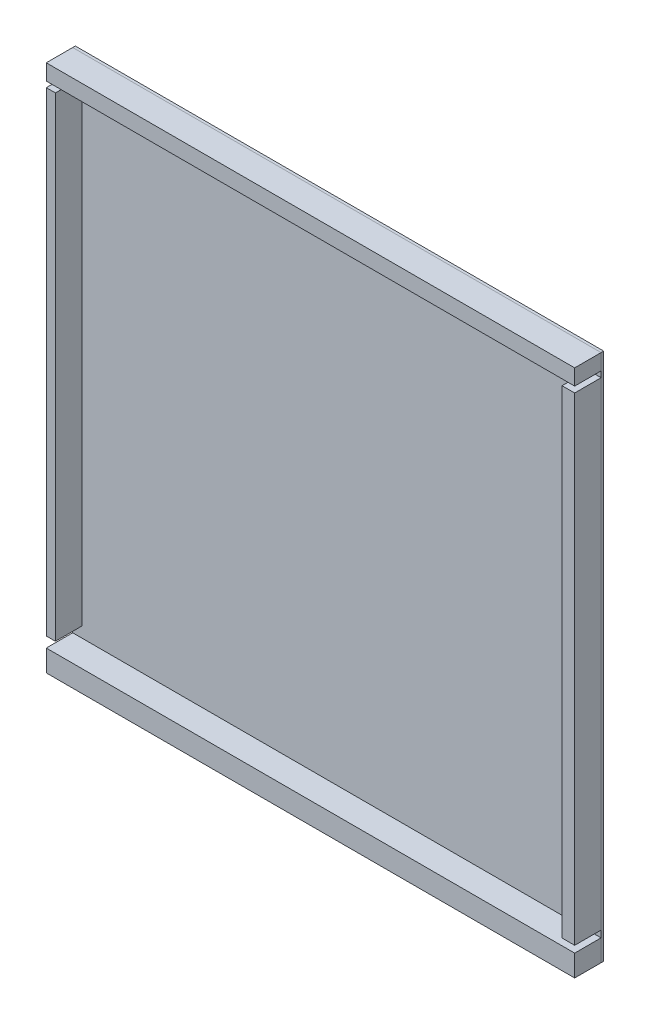
SolidWorks part; units mm, degrees
other "COLL.BOX-Boss-Extrude2"
other "COLL.BOX-Boss-Extrude3"
other "COLL.BOX-Boss-Extrude4"
other "COLL.BOX-Boss-Extrude5"
other "COLL.BOX-Boss-Extrude6"
ref_plane "Front Plane" through (0, 0, 0) normal (0, 0, 1) x (1, 0, 0)
ref_plane "Top Plane" through (0, 0, 0) normal (0, 1, 0) x (1, 0, 0)
ref_plane "Right Plane" through (0, 0, 0) normal (1, 0, 0) x (0, 0, -1)
sketch "Sketch1" plane through (0, 0, 0) normal (0, 0, 1) x (1, 0, 0)
  line L1 (-250, 1750) -> (1750, 1750)
  line L2 (-250, 1750) -> (-250, -250)
  line L3 (-250, -250) -> (1750, -250)
  line L4 (1750, 1750) -> (1750, -250)
  dimension "D1" = 2000
  dimension "D2" = 2000
  dimension "D3" = 250
  dimension "D4" = 250
extrude "Boss-Extrude1" add sketch "Sketch1" along normal blind 10
sketch "Sketch2" plane through (0, 0, 10) normal (0, 0, 1) x (1, 0, 0)
  line L1 (-250, 1750) -> (1750, 1750)
  line L2 (-250, 1750) -> (-250, -250)
  line L3 (-250, -250) -> (1750, -250)
  line L4 (1750, 1750) -> (1750, -250)
extrude "Boss-Extrude2" add sketch "Sketch2" against normal up to next (10 mm away) separate body
sketch "Sketch3" plane through (0, 0, 10) normal (0, 0, 1) x (1, 0, 0)
  line L0 (1750, -250) -> (1750, 1750) construction
  line L1 (-250, 1750) -> (1750, 1750)
  line L2 (-250, 1750) -> (-250, 1690.1338)
  line L3 (-250, 1690.1338) -> (1750, 1690.1338)
  line L4 (1750, 1750) -> (1750, 1690.1338)
extrude "Boss-Extrude3" add sketch "Sketch3" along normal blind 100 separate body
sketch "Sketch4" plane through (0, 0, 10) normal (0, 0, 1) x (1, 0, 0)
  line L0 (-250, 1750) -> (-250, -250) construction
  line L1 (1750, -250) -> (-250, -250)
  line L2 (1750, -250) -> (1750, -168.4149)
  line L3 (1750, -168.4149) -> (-250, -168.4149)
  line L4 (-250, -250) -> (-250, -168.4149)
extrude "Boss-Extrude4" add sketch "Sketch4" along normal blind 100 separate body
sketch "Sketch5" plane through (0, 0, 10) normal (0, 0, 1) x (1, 0, 0)
  line L0 (1750, -250) -> (1750, 1750) construction
  line L1 (1750, 1667.6151) -> (1702.2657, 1667.6151)
  line L2 (1750, 1667.6151) -> (1750, -142.8735)
  line L3 (1750, -142.8735) -> (1702.2657, -142.8735)
  line L4 (1702.2657, 1667.6151) -> (1702.2657, -142.8735)
extrude "Boss-Extrude5" add sketch "Sketch5" along normal blind 100 separate body
sketch "Sketch6" plane through (0, 0, 10) normal (0, 0, 1) x (1, 0, 0)
  line L0 (-250, 1750) -> (-250, -250) construction
  line L1 (-250, 1668.5491) -> (-215.3578, 1668.5491)
  line L2 (-250, 1668.5491) -> (-250, -128.9914)
  line L3 (-250, -128.9914) -> (-215.3578, -128.9914)
  line L4 (-215.3578, 1668.5491) -> (-215.3578, -128.9914)
extrude "Boss-Extrude6" add sketch "Sketch6" along normal blind 100 separate body
